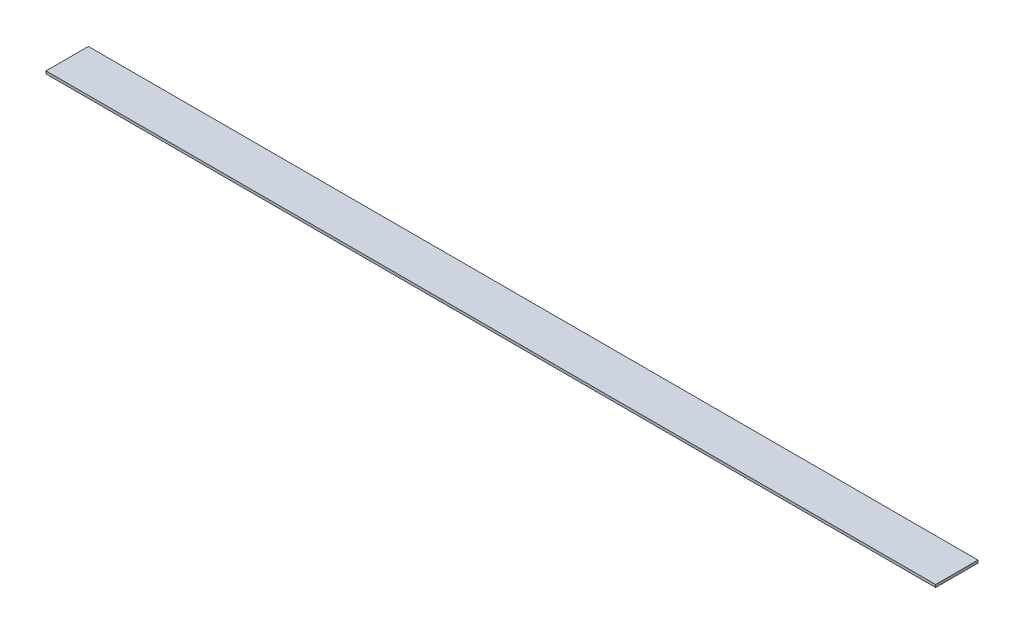
SolidWorks part; units mm, degrees
material "Nylon 101"
ref_plane "Front Plane" through (0, 0, 0) normal (0, 0, 1) x (1, 0, 0)
ref_plane "Top Plane" through (0, 0, 0) normal (0, 1, 0) x (1, 0, 0)
ref_plane "Right Plane" through (0, 0, 0) normal (1, 0, 0) x (0, 0, -1)
sketch "Sketch1" plane through (0, 0, 0) normal (0, 1, 0) x (1, 0, 0)
  line L1 (0, 0) -> (533.4, 0)
  line L2 (0, 0) -> (0, 25.4)
  line L3 (0, 25.4) -> (533.4, 25.4)
  line L4 (533.4, 0) -> (533.4, 25.4)
  dimension "D1" = 25.4
  dimension "D2" = 533.4
extrude "Boss-Extrude1" add sketch "Sketch1" along normal blind 1.5875
